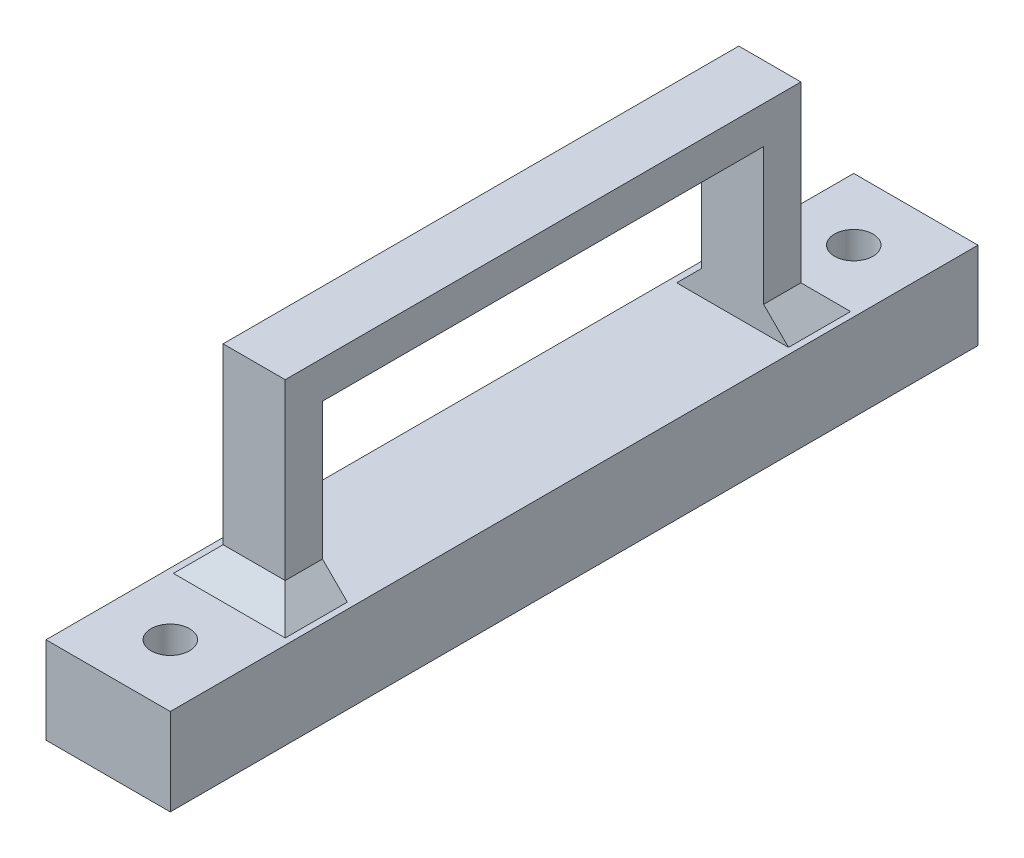
SolidWorks part; units mm, degrees
material "PET-G 50%"
ref_plane "Front Plane" through (0, 0, 0) normal (0, 0, 1) x (1, 0, 0)
ref_plane "Top Plane" through (0, 0, 0) normal (0, 1, 0) x (1, 0, 0)
ref_plane "Right Plane" through (0, 0, 0) normal (1, 0, 0) x (0, 0, -1)
sketch "Sketch1" plane through (0, 0, 0) normal (0, 1, 0) x (1, 0, 0)
  line L4 (5, 60) -> (5, 5) construction
  line L5 (0, 0) -> (10, 0)
  line L6 (0, 0) -> (0, 65)
  line L7 (0, 65) -> (10, 65)
  line L8 (10, 0) -> (10, 65)
  circle A0 centre (5, 60) radius 1.55
  circle A1 centre (5, 5) radius 1.55
  point P2 (5, 32.5)
  point P24 (0, 32.5)
  dimension "D1" = 3.1
  dimension "D2" = 3.1
  dimension "D3" = 55
  dimension "D6" = 65
  dimension "D7" = 10
  dimension "D8" = 5
extrude "Boss-Extrude1" add sketch "Sketch1" along normal blind 7
sketch "Sketch2" plane through (0, 7, 0) normal (0, 1, 0) x (1, 0, 0)
  line L1 (7.5, 53.25) -> (2.5, 53.25)
  line L2 (7.5, 53.25) -> (7.5, 50.25)
  line L3 (7.5, 50.25) -> (2.5, 50.25)
  line L4 (2.5, 53.25) -> (2.5, 50.25)
  line L5 (7.5, 11.75) -> (2.5, 11.75)
  line L6 (7.5, 11.75) -> (7.5, 14.75)
  line L7 (7.5, 14.75) -> (2.5, 14.75)
  line L8 (2.5, 11.75) -> (2.5, 14.75)
  line L9 (2.5, 50.25) -> (2.5, 14.75) construction
  line L10 (0, 65) -> (0, 0) construction
  line L11 (10, 65) -> (0, 65) construction
  point P12 (0, 32.5)
  point P15 (2.5, 32.5)
  point P18 (5, 65)
  point P19 (5, 53.25)
  dimension "D1" = 3
  dimension "D2" = 5
  dimension "D3" = 35.5
extrude "Boss-Extrude2" add sketch "Sketch2" along normal blind 16
sketch "Sketch3" plane through (0, 0, -50.25) normal (0, 0, 1) x (1, 0, 0)
  line L0 (7.5, 23) -> (7.5, 7) construction
  line L1 (2.5, 23) -> (7.5, 23)
  line L2 (2.5, 23) -> (2.5, 20)
  line L3 (2.5, 20) -> (7.5, 20)
  line L4 (7.5, 23) -> (7.5, 20)
  dimension "D1" = 3
extrude "Boss-Extrude3" add sketch "Sketch3" along normal blind 35.5
chamfer "Chamfer1" distance 2 angle 45 6 edges at (2.5, 7, -51.75) (2.5, 7, -13.25) (7.5, 7, -13.25) (5, 7, -11.75) (7.5, 7, -51.75) (5, 7, -53.25)
